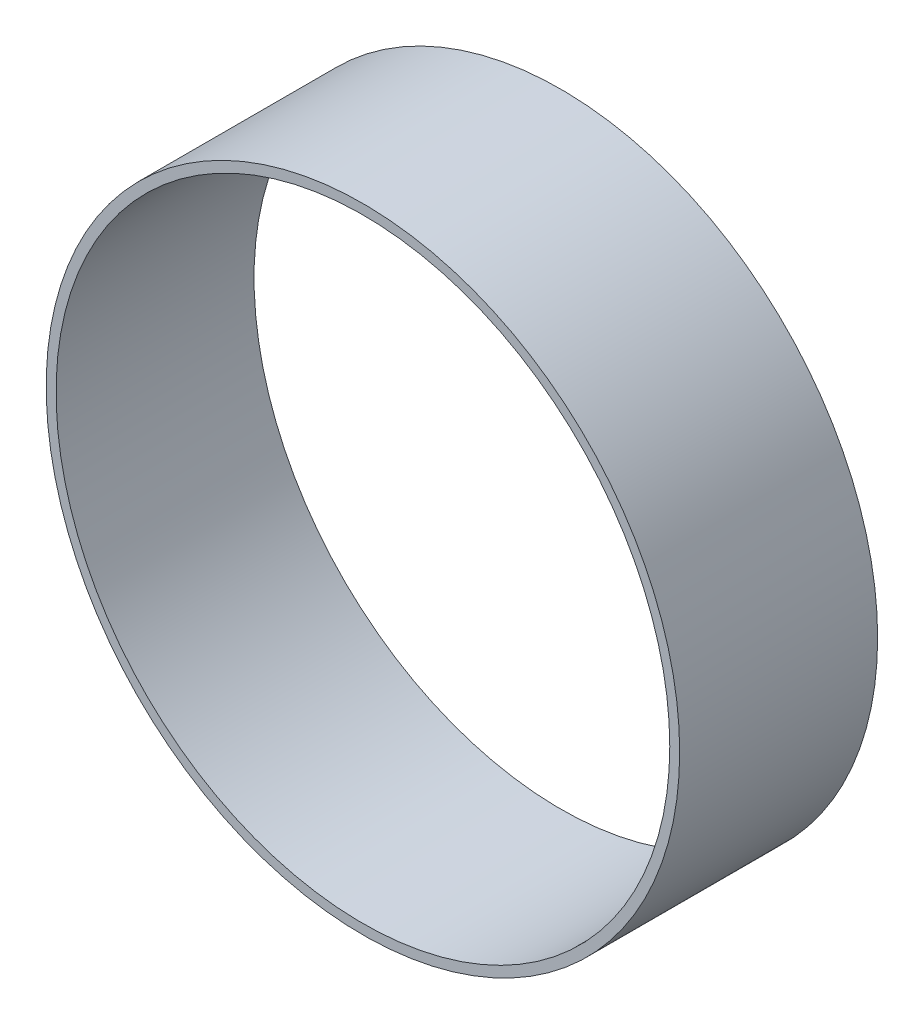
SolidWorks part; units mm, degrees
ref_plane "Plan de face" through (0, 0, 0) normal (0, 0, 1) x (1, 0, 0)
ref_plane "Plan de dessus" through (0, 0, 0) normal (0, 1, 0) x (1, 0, 0)
ref_plane "Plan de droite" through (0, 0, 0) normal (1, 0, 0) x (0, 0, -1)
sketch "Esquisse1" plane through (0, 0, 0) normal (0, 0, 1) x (1, 0, 0)
  circle A0 centre (0, 0) radius 80
  dimension "D1" = 160
extrude "Boss.-Extru.1" add sketch "Esquisse1" along normal blind 50
sketch "Esquisse2" plane through (0, 0, 50) normal (0, 0, 1) x (1, 0, 0)
  circle A0 centre (0, 0) radius 77.5
  dimension "D1" = 155
extrude "Enlèv. mat.-Extru.1" cut sketch "Esquisse2" against normal blind 50
